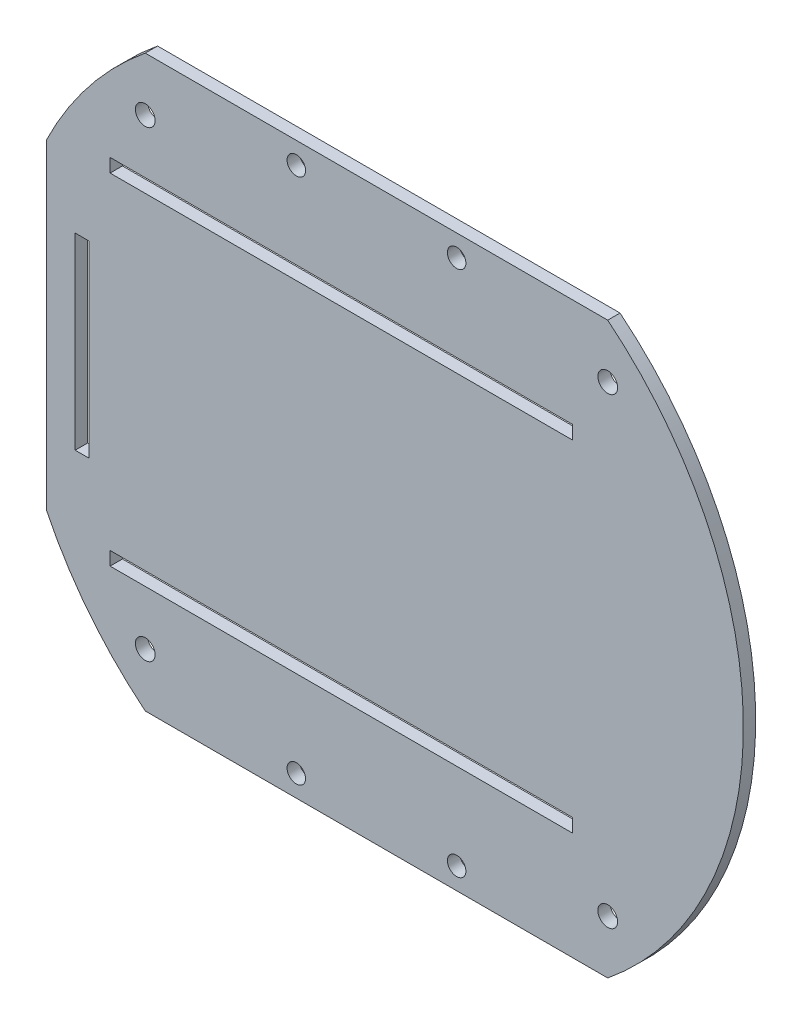
SolidWorks part; units mm, degrees
ref_plane "Ebene vorne" through (0, 0, 0) normal (0, 0, 1) x (1, 0, 0)
ref_plane "Ebene oben" through (0, 0, 0) normal (0, 1, 0) x (1, 0, 0)
ref_plane "Ebene rechts" through (0, 0, 0) normal (1, 0, 0) x (0, 0, -1)
sketch "Skizze1" plane through (0, 0, 0) normal (0, 0, 1) x (1, 0, 0)
  circle A0 centre (0, 0) radius 59.5
  dimension "D1" = 119
extrude "Aufsatz-Linear austragen1" add sketch "Skizze1" along normal blind 2
sketch "Skizze2" plane through (0, 0, 2) normal (0, 0, 1) x (1, 0, 0)
  line L0 (-43.1972, 26.5) -> (31.8028, -26.5) construction
  line L1 (-43.1972, 28.7) -> (31.8028, 28.7)
  line L2 (-43.1972, 28.7) -> (-43.1972, 26.5)
  line L3 (-43.1972, 26.5) -> (31.8028, 26.5)
  line L4 (31.8028, 28.7) -> (31.8028, 26.5)
  line L5 (-43.1972, -26.5) -> (31.8028, -26.5)
  line L6 (-43.1972, -26.5) -> (-43.1972, -28.7)
  line L7 (-43.1972, -28.7) -> (31.8028, -28.7)
  line L8 (31.8028, -26.5) -> (31.8028, -28.7)
  line L9 (31.8028, 26.5) -> (-43.1972, -26.5) construction
  line L10 (-48.8589, 15.25) -> (-48.8589, 26.5) construction
  line L11 (-48.8589, 15.25) -> (-46.6589, 15.25)
  line L12 (-48.8589, 15.25) -> (-48.8589, -15.25)
  line L13 (-48.8589, -15.25) -> (-46.6589, -15.25)
  line L14 (-46.6589, 15.25) -> (-46.6589, -15.25)
  line L15 (-48.8589, -15.25) -> (-48.8589, -26.5) construction
  line L16 (-43.1972, -28.7) -> (-52.1206, -28.7) construction
  line L19 (-43.1972, 28.7) -> (-52.1206, 28.7) construction
  line L20 (31.8028, -28.7) -> (52.1206, -28.7) construction
  line L21 (31.8028, 28.7) -> (52.1206, 28.7) construction
  line L22 (-48.8589, -15.25) -> (-57.5125, -15.25) construction
  line L23 (-48.8589, 15.25) -> (-57.5125, 15.25) construction
  line L24 (37.5, -37.5) -> (-37.5, -37.5) construction
  line L25 (-37.5, -37.5) -> (-37.5, 37.5) construction
  line L26 (-37.5, 37.5) -> (37.5, 37.5) construction
  line L27 (37.5, 37.5) -> (37.5, -37.5) construction
  line L28 (-37.5, 37.5) -> (37.5, -37.5) construction
  line L29 (37.5, 37.5) -> (-37.5, -37.5) construction
  circle A1 centre (37.5, -37.5) radius 1.6
  circle A2 centre (-37.5, -37.5) radius 1.6
  circle A4 centre (0, 0) radius 59.5 construction
  circle A5 centre (-37.5, 37.5) radius 1.6
  circle A6 centre (37.5, 37.5) radius 1.6
  point P8 (0, 0)
  point P10 (-5.6972, 0)
  point P33 (-5.6972, 0)
  point P37 (0, 0)
  dimension "D8" = 3.2
  dimension "D11" = 3.2
  dimension "D12" = 3.2
  dimension "D13" = 3.2
  dimension "D1" = 75
  dimension "D2" = 2.2
  dimension "D3" = 2.2
  dimension "D4" = 53
  dimension "D5" = 2.2
  dimension "D6" = 8.6536
  dimension "D7" = 20.3178
  dimension "D9" = 20.3178
  dimension "D10" = 30.5
  dimension "D14" = 75
  dimension "D15" = 75
extrude "Schnitt-Linear austragen1" cut sketch "Skizze2" against normal up to surface (2 mm away) up to face at (59.5, 0, 0)
sketch "Skizze3" plane through (0, 0, 2) normal (0, 0, 1) x (1, 0, 0)
  line L0 (-13, 42.7) -> (-13, -42.7) construction
  line L1 (-46.6589, -15.25) -> (-46.6589, 15.25) construction
  line L2 (-13, 42.7) -> (13, 42.7) construction
  line L3 (-13, -42.7) -> (13, -42.7) construction
  line L4 (13, 42.7) -> (13, 28.7) construction
  line L5 (31.8028, 28.7) -> (-43.1972, 28.7) construction
  line L6 (13, -42.7) -> (13, -28.7) construction
  line L7 (-43.1972, -28.7) -> (31.8028, -28.7) construction
  line L8 (-29.581, 46.1952) -> (-29.581, 28.7) construction
  line L9 (-13, -42.7) -> (13, 42.7) construction
  line L10 (-37.5, 59.5) -> (37.5, 59.5)
  line L11 (-37.5, 59.5) -> (-37.5, 46.1952)
  line L12 (-37.5, 46.1952) -> (37.5, 46.1952)
  line L13 (37.5, 59.5) -> (37.5, 46.1952)
  line L14 (-37.5, -46.1952) -> (37.5, -46.1952)
  line L15 (-37.5, -46.1952) -> (-37.5, -59.5)
  line L16 (-37.5, -59.5) -> (37.5, -59.5)
  line L17 (37.5, -46.1952) -> (37.5, -59.5)
  line L18 (-13.4982, -28.7) -> (-13.4982, -46.1952) construction
  line L20 (-53.5187, 26) -> (-59.5, 26)
  line L21 (-53.5187, 26) -> (-53.5187, -26)
  line L22 (-53.5187, -26) -> (-59.5, -26)
  line L23 (-59.5, 26) -> (-59.5, -26)
  line L24 (-43.1972, 28.7) -> (-43.1972, 26.5) construction
  circle A0 centre (-13, -42.7) radius 1.5
  circle A1 centre (13, -42.7) radius 1.5
  circle A2 centre (-13, 42.7) radius 1.5
  circle A3 centre (13, 42.7) radius 1.5
  circle A4 centre (0, 0) radius 59.5 construction
  point P10 (0, 0)
  dimension "D1" = 3
  dimension "D2" = 3
  dimension "D3" = 3
  dimension "D4" = 3
  dimension "D5" = 26
  dimension "D6" = 26
  dimension "D7" = 52
  dimension "D8" = 14
  dimension "D9" = 75
  dimension "D10" = 13.6162
  dimension "D11" = 24.0018
extrude "Schnitt-Linear austragen2" cut sketch "Skizze3" against normal up to surface (2 mm away) up to face at (39.1, 37.5, 0)
